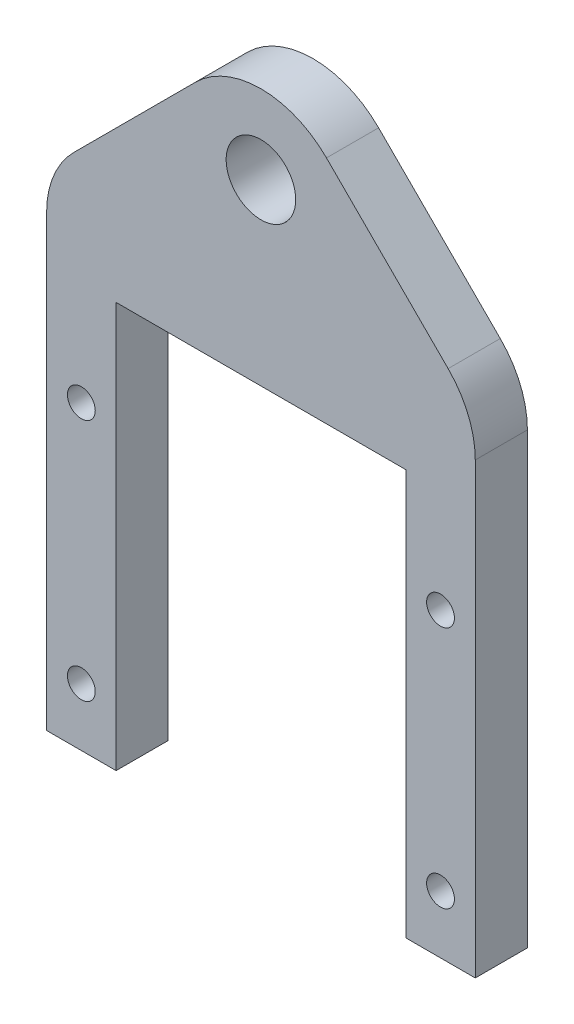
SolidWorks part; units mm, degrees
ref_plane "前视基准面" through (0, 0, 0) normal (0, 0, 1) x (1, 0, 0)
ref_plane "上视基准面" through (0, 0, 0) normal (0, 1, 0) x (1, 0, 0)
ref_plane "右视基准面" through (0, 0, 0) normal (1, 0, 0) x (0, 0, -1)
sketch "草图1" plane through (0, 0, 0) normal (0, 0, 1) x (1, 0, 0)
  line L0 (-12.5, 0) -> (-18.5, 0)
  line L2 (-12.5, 0) -> (-12.5, 35)
  line L3 (-12.5, 35) -> (12.5, 35)
  line L4 (12.5, 0) -> (12.5, 35)
  line L5 (-18.5, 0) -> (-18.5, 42.0349)
  line L6 (-18.5, 42.0349) -> (0, 60.5349)
  line L7 (0, 60.5349) -> (18.5, 42.0349)
  line L8 (18.5, 42.0349) -> (18.5, 0)
  line L9 (18.5, 0) -> (12.5, 0)
  line L10 (0, 60.5349) -> (0, 0) construction
  circle A0 centre (0, 50.4214) radius 3
  circle A2 centre (-15.5, 5) radius 1.2
  circle A3 centre (-15.5, 26) radius 1.2
  circle A4 centre (15.5, 5) radius 1.2
  circle A5 centre (15.5, 26) radius 1.2
  point P27 (0, 35)
extrude "凸台-拉伸1" add sketch "草图1" along normal blind 4.5
fillet "圆角1" radius 8 3 edges at (-18.5, 42.0349, 2.25) (18.5, 42.0349, 2.25) (0, 60.5349, 2.25)
